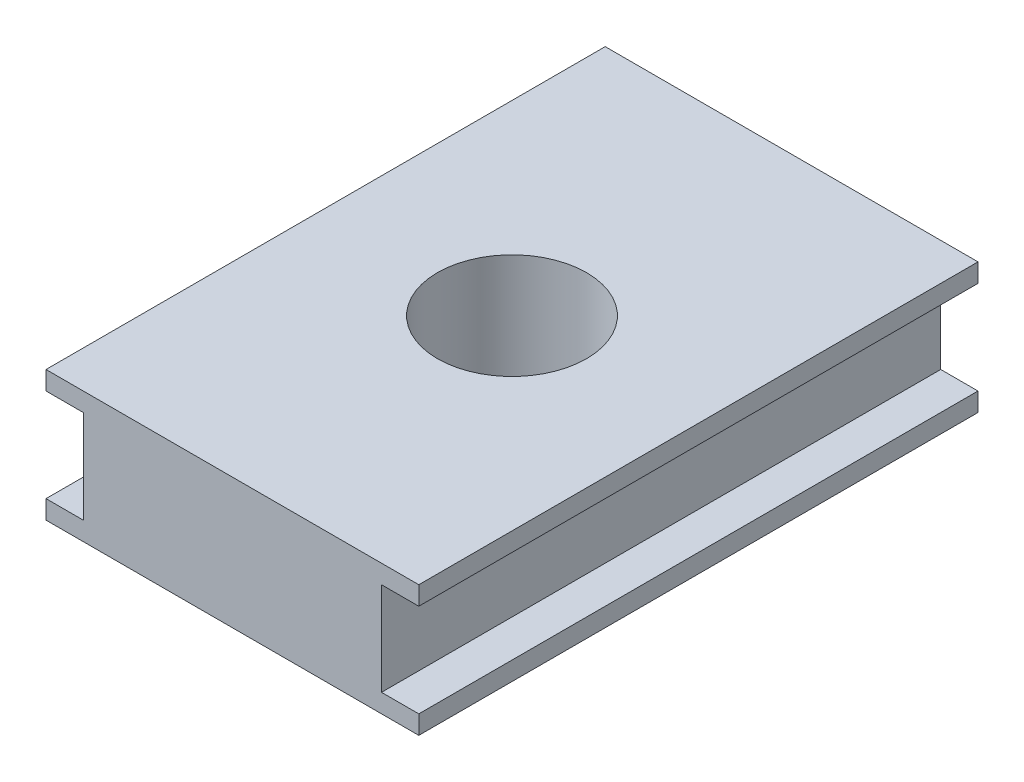
SolidWorks part; units mm, degrees
ref_plane "Front Plane" through (0, 0, 0) normal (0, 0, 1) x (1, 0, 0)
ref_plane "Top Plane" through (0, 0, 0) normal (0, 1, 0) x (1, 0, 0)
ref_plane "Right Plane" through (0, 0, 0) normal (1, 0, 0) x (0, 0, -1)
sketch "Sketch1" plane through (0, 0, 0) normal (0, 1, 0) x (1, 0, 0)
  line L1 (-10, -15) -> (10, -15)
  line L2 (-10, -15) -> (-10, 15)
  line L3 (-10, 15) -> (10, 15)
  line L4 (10, -15) -> (10, 15)
  line L5 (-10, -15) -> (10, 15) construction
  line L6 (-10, 15) -> (10, -15) construction
  point P0 (0, 0)
  dimension "D1" = 20
  dimension "D2" = 30
extrude "Boss-Extrude1" add sketch "Sketch1" along normal blind 7
sketch "Sketch2" plane through (10, 0, 0) normal (1, 0, 0) x (0, 0, -1)
  line L0 (15, 7) -> (15, 0) construction
  line L1 (-15, 1) -> (15, 1)
  line L2 (-15, 1) -> (-15, 6)
  line L3 (-15, 6) -> (15, 6)
  line L4 (15, 1) -> (15, 6)
  line L5 (-15, 1) -> (15, 6) construction
  line L6 (-15, 6) -> (15, 1) construction
  line L7 (-15, 7) -> (15, 7) construction
  line L8 (-15, 0) -> (15, 0) construction
  point P0 (0, 3.5)
  dimension "D1" = 1
  dimension "D2" = 1
extrude "Cut-Extrude1" cut sketch "Sketch2" against normal blind 2
sketch "Sketch3" plane through (-10, 0, 0) normal (-1, 0, 0) x (0, 0, 1)
  line L0 (15, 7) -> (15, 0) construction
  line L1 (-15, 1) -> (15, 1)
  line L2 (-15, 1) -> (-15, 6)
  line L3 (-15, 6) -> (15, 6)
  line L4 (15, 1) -> (15, 6)
  line L5 (-15, 1) -> (15, 6) construction
  line L6 (-15, 6) -> (15, 1) construction
  line L7 (-15, 7) -> (15, 7) construction
  line L8 (-15, 0) -> (15, 0) construction
  point P0 (0, 3.5)
  dimension "D1" = 1
  dimension "D2" = 1
extrude "Cut-Extrude2" cut sketch "Sketch3" against normal blind 2
sketch "Sketch4" plane through (0, 7, 0) normal (0, 1, 0) x (1, 0, 0)
  circle A0 centre (0, 0) radius 4
extrude "Cut-Extrude3" cut sketch "Sketch4" against normal blind 10
